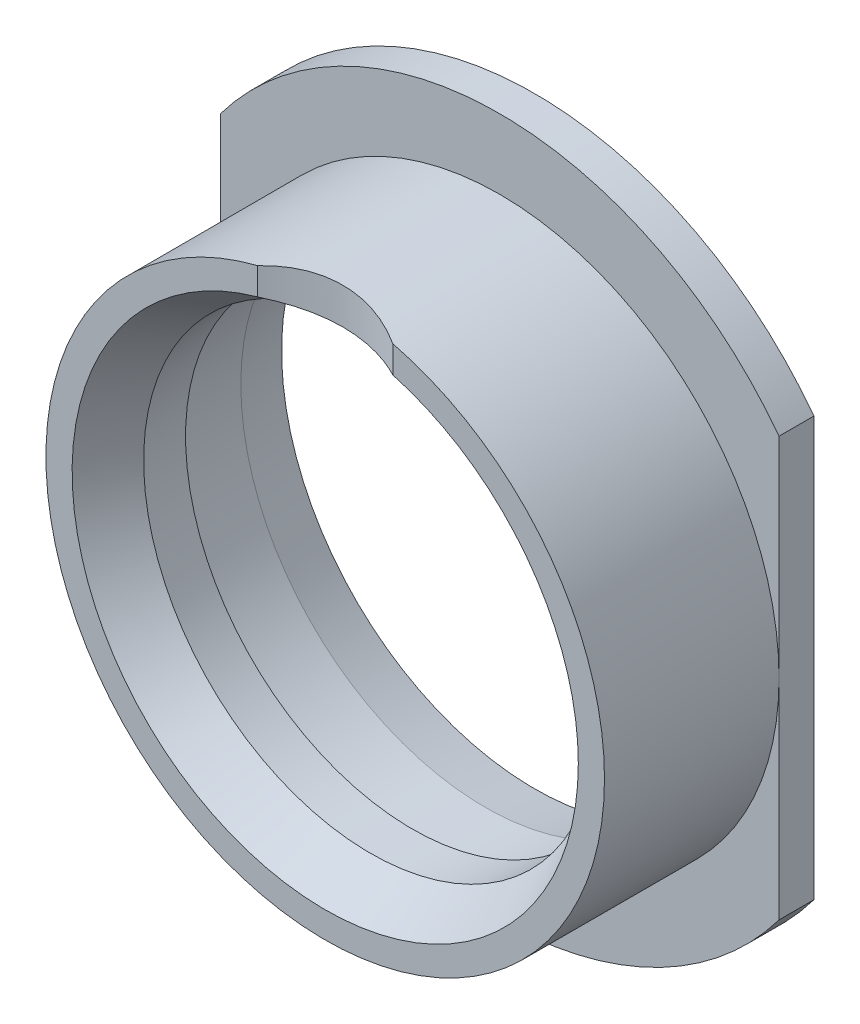
SolidWorks part; units mm, degrees
material "AISI 316 Нержавеющая сталь, лист (SS)"
ref_plane "Front" through (0, 0, 0) normal (0, 0, 1) x (1, 0, 0)
ref_plane "Top" through (0, 0, 0) normal (0, 1, 0) x (1, 0, 0)
ref_plane "Right" through (0, 0, 0) normal (1, 0, 0) x (0, 0, -1)
sketch "Эскиз1" plane through (0, 0, 0) normal (1, 0, 0) x (0, 0, -1)
  line L0 (2.5981, 13) -> (5, 13)
  line L1 (9.1644, 14) -> (12, 14.5)
  line L2 (12, 14.5) -> (12, 20)
  line L3 (12, 20) -> (10, 20)
  line L4 (10, 20) -> (10, 16)
  line L5 (10, 16) -> (0, 16)
  line L6 (0, 16) -> (0, 14.5)
  line L7 (0, 0) -> (12.5997, 0) construction
  line L8 (5, 14) -> (9.1644, 14)
  line L9 (5, 13) -> (5, 14)
  line L10 (0, 14.5) -> (2.5981, 13)
  dimension "D1" = 26
  dimension "D2" = 32
  dimension "D3" = 40
  dimension "D4" = 12
  dimension "D5" = 2
  dimension "D6" = 10
  dimension "D7" = 29
  dimension "D8" = 28
  dimension "D9" = 7
  dimension "D10" = 30
  dimension "D11" = 29
revolve "Повернуть1" add sketch "Эскиз1" angle 360 about L7
sketch "Эскиз2" plane through (0, 0, -10) normal (0, 0, 1) x (1, 0, 0)
  line L0 (-16, 12) -> (-16, -12)
  line L1 (16, 12) -> (16, -12)
  circle A0 centre (0, 0) radius 20 construction
  circle A1 centre (0, 0) radius 16 construction
  circle A2 centre (0, 0) radius 16 construction
  circle M2 centre (0, 0) radius 20
extrude "Вырез-Вытянуть1" cut sketch "Эскиз2" against normal through all and the other way through all contours L0 M2 | L1 M2
sketch "Эскиз3" plane through (0, 0, 0) normal (0, 1, 0) x (1, 0, 0)
  line L0 (-16, 0) -> (16, 0) construction
  line L1 (0, 1) -> (4.2996, 1) construction
  arc A0 (-3.873, 0) -> (3.873, 0) centre (0, -7) cw
  dimension "D1" = 8
  dimension "D2" = 1
extrude "Вырез-Вытянуть2" cut sketch "Эскиз3" along normal through all flip side to cut
